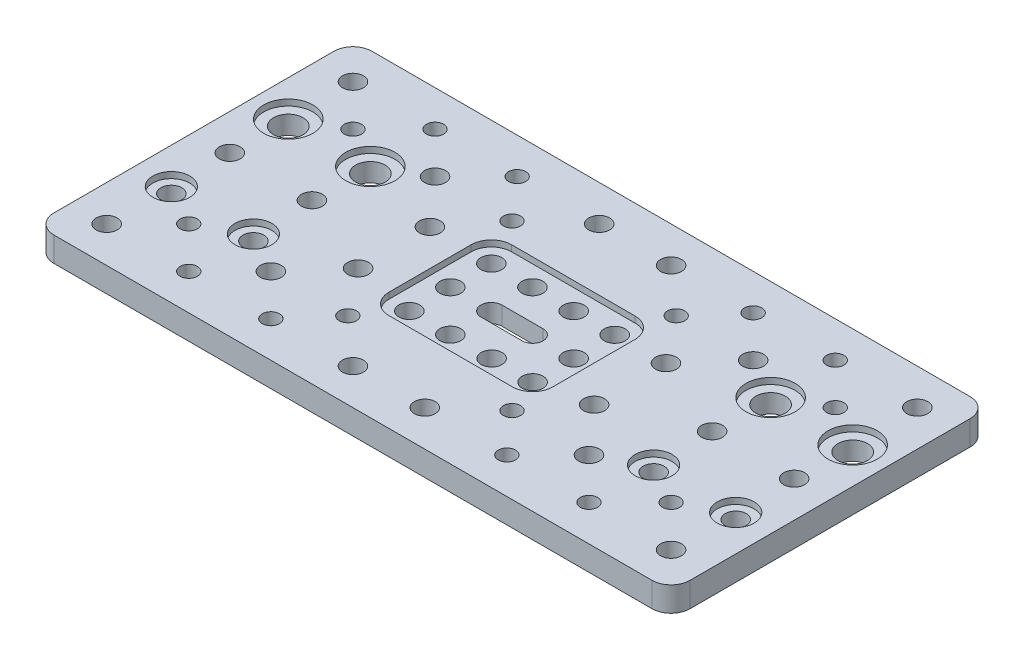
SolidWorks part; units mm, degrees
material "6061-T6 (SS)"
ref_plane "Front Plane" through (0, 0, 0) normal (0, 0, 1) x (1, 0, 0)
ref_plane "Top Plane" through (0, 0, 0) normal (0, 1, 0) x (1, 0, 0)
ref_plane "Right Plane" through (0, 0, 0) normal (1, 0, 0) x (0, 0, -1)
sketch "Sketch1" plane through (0, 0, 0) normal (0, 1, 0) x (1, 0, 0)
  line L1 (4.64, 0) -> (150.38, 0)
  line L2 (0, 4.64) -> (0, 72.88)
  line L3 (4.64, 77.52) -> (150.38, 77.52)
  line L4 (155.02, 4.64) -> (155.02, 72.88)
  arc A0 (150.38, 0) -> (155.02, 4.64) centre (150.38, 4.64) ccw
  arc A1 (150.38, 77.52) -> (155.02, 72.88) centre (150.38, 72.88) cw
  arc A2 (0, 72.88) -> (4.64, 77.52) centre (4.64, 72.88) cw
  arc A3 (4.64, 0) -> (0, 4.64) centre (4.64, 4.64) cw
  point P9 (155.02, 77.52)
  point P12 (0, 77.52)
  point P15 (0, 0)
  dimension "D3" = 4.64
  dimension "D1" = 77.52
  dimension "D2" = 155.02
extrude "Boss-Extrude1" add sketch "Sketch1" along normal blind 6
hole_wizard "Ø5.1 (5.1) Diameter Hole1" positions "Sketch3" profile "Sketch2" hole size "Ø5.1" standard "ANSI Metric" end condition through all
sketch "Sketch3" plane through (0, 6, 0) normal (0, 1, 0) x (1, 0, 0)
  line L0 (0, 38.76) -> (77.51, 38.76) construction
  line L1 (0, 72.88) -> (0, 4.64) construction
  line L2 (77.51, 38.76) -> (77.51, 77.52) construction
  line L3 (150.38, 77.52) -> (4.64, 77.52) construction
  point P0 (8.755, 68.76)
  point P2 (8.755, 38.76)
  point P4 (28.755, 38.76)
  point P6 (38.755, 58.76)
  point P8 (48.755, 47.515)
  point P10 (68.755, 68.76)
  point P12 (62.485, 48.76)
  point P14 (72.485, 48.76)
  point P16 (62.485, 38.76)
  point P36 (92.535, 38.76)
  point P37 (82.535, 48.76)
  point P38 (92.535, 48.76)
  point P39 (86.265, 68.76)
  point P40 (106.265, 47.515)
  point P41 (116.265, 58.76)
  point P42 (126.265, 38.76)
  point P43 (146.265, 38.76)
  point P44 (146.265, 68.76)
  point P47 (146.265, 8.76)
  point P48 (116.265, 18.76)
  point P49 (106.265, 30.005)
  point P50 (92.535, 28.76)
  point P51 (82.535, 28.76)
  point P52 (86.265, 8.76)
  point P53 (68.755, 8.76)
  point P54 (72.485, 28.76)
  point P55 (62.485, 28.76)
  point P56 (48.755, 30.005)
  point P57 (38.755, 18.76)
  point P58 (8.755, 8.76)
  dimension "D1" = 10
  dimension "D2" = 10
  dimension "D3" = 17.51
  dimension "D4" = 30
  dimension "D5" = 30
  dimension "D6" = 20
  dimension "D7" = 10.05
  dimension "D8" = 17.51
  dimension "D9" = 60
  dimension "D10" = 20
  dimension "D11" = 10
sketch "Sketch2" plane through (8.755, 6, -68.76) normal (1, 0, 0) x (0, 0, 1)
  line L0 (0, 0) -> (0, 6)
  line L1 (0, 6) -> (2.55, 6)
  line L2 (2.55, 6) -> (2.55, 0)
  line L5 (2.55, 0) -> (0, 0)
  line L11 (0, -6.35) -> (0, 107.95) construction
  dimension "Thru Hole Dia." = 5.1
  dimension "Thru Hole Depth" = 6
hole_wizard "M5x0.8 Tapped Hole1" positions "Sketch5" profile "Sketch4" tap size "M5x0.8" standard "ANSI Metric" end condition through all
sketch "Sketch5" plane through (0, 6, 0) normal (0, 1, 0) x (1, 0, 0)
  line L0 (0, 38.76) -> (77.51, 38.76) construction
  line L1 (0, 72.88) -> (0, 4.64) construction
  line L2 (77.51, 38.76) -> (77.51, 77.52) construction
  line L3 (150.38, 77.52) -> (4.64, 77.52) construction
  circle A0 centre (8.755, 68.76) radius 2.55 construction
  point P0 (18.75, 58.76)
  point P2 (28.755, 68.76)
  point P4 (48.755, 68.76)
  point P6 (57.51, 58.76)
  point P23 (48.755, 8.76)
  point P24 (57.51, 18.76)
  point P25 (18.75, 18.76)
  point P26 (28.755, 8.76)
  point P28 (106.265, 68.76)
  point P29 (97.51, 58.76)
  point P30 (97.51, 18.76)
  point P31 (106.265, 8.76)
  point P32 (126.265, 8.76)
  point P33 (136.27, 18.76)
  point P34 (126.265, 68.76)
  point P35 (136.27, 58.76)
  dimension "D5" = 20
  dimension "D1" = 20
  dimension "D2" = 40
  dimension "D3" = 60
  dimension "D4" = 40
  dimension "D6" = 38.76
sketch "Sketch4" plane through (18.75, 6, -58.76) normal (1, 0, 0) x (0, 0, 1)
  line L0 (0, 0) -> (0, 6)
  line L1 (0, 6) -> (2.1, 6)
  line L2 (2.1, 6) -> (2.1, 0)
  line L5 (2.1, 0) -> (0, 0)
  line L11 (0, -6.35) -> (0, 107.95) construction
  dimension "Thread Major Dia." = 4.2
  dimension "Thru Tap Drill Depth" = 6
sketch "Sketch6" plane through (0, 6, 0) normal (0, 1, 0) x (1, 0, 0)
  line L0 (77.51, 77.52) -> (77.51, 95.8918) construction
  line L1 (150.38, 77.52) -> (4.64, 77.52) construction
  line L2 (0, 38.76) -> (-8.4214, 38.76) construction
  line L3 (0, 72.88) -> (0, 4.64) construction
  line L4 (8.755, 68.76) -> (8.755, 53.01) construction
  circle A0 centre (8.755, 53.01) radius 3.6
  circle A1 centre (28.755, 53.01) radius 3.6
  circle A2 centre (8.755, 24.51) radius 2.55
  circle A3 centre (28.755, 24.51) radius 2.55
  circle A4 centre (126.265, 24.51) radius 2.55
  circle A5 centre (146.265, 24.51) radius 2.55
  circle A6 centre (126.265, 53.01) radius 3.6
  circle A7 centre (146.265, 53.01) radius 3.6
  dimension "D1" = 7.2
  dimension "D2" = 5.1
  dimension "D3" = 28.5
  dimension "D4" = 20
extrude "Cut-Extrude1" cut sketch "Sketch6" against normal through all
sketch "Sketch7" plane through (0, 6, 0) normal (0, 1, 0) x (1, 0, 0)
  line L0 (77.51, 77.52) -> (77.51, 38.76) construction
  line L1 (150.38, 77.52) -> (4.64, 77.52) construction
  line L2 (57.535, 23.81) -> (97.485, 53.71) construction
  line L3 (62.475, 53.71) -> (92.545, 53.71)
  line L4 (57.535, 48.77) -> (57.535, 28.75)
  line L5 (62.475, 23.81) -> (92.545, 23.81)
  line L6 (97.485, 48.77) -> (97.485, 28.75)
  line L7 (77.51, 38.76) -> (155.02, 38.76) construction
  line L8 (155.02, 4.64) -> (155.02, 72.88) construction
  circle A0 centre (8.755, 53.01) radius 6
  circle A1 centre (28.755, 53.01) radius 6
  circle A2 centre (8.755, 24.51) radius 4.5
  circle A3 centre (28.755, 24.51) radius 4.5
  circle A4 centre (126.265, 24.51) radius 4.5
  circle A5 centre (146.265, 24.51) radius 4.5
  circle A6 centre (126.265, 53.01) radius 6
  circle A7 centre (146.265, 53.01) radius 6
  arc A8 (92.545, 53.71) -> (97.485, 48.77) centre (92.545, 48.77) cw
  arc A9 (62.475, 53.71) -> (57.535, 48.77) centre (62.475, 48.77) ccw
  arc A10 (57.535, 28.75) -> (62.475, 23.81) centre (62.475, 28.75) ccw
  arc A11 (92.545, 23.81) -> (97.485, 28.75) centre (92.545, 28.75) ccw
  point P28 (77.51, 38.76)
  dimension "D1" = 12
  dimension "D2" = 9
  dimension "D5" = 4.94
  dimension "D3" = 39.95
  dimension "D4" = 29.9
extrude "Cut-Extrude2" cut sketch "Sketch7" against normal blind 1.5
sketch "Sketch8" plane through (0, 4.5, 0) normal (0, 1, 0) x (1, 0, 0)
  line L0 (72.485, 38.76) -> (82.535, 38.76) construction
  line L1 (72.485, 41.31) -> (82.535, 41.31)
  line L2 (72.485, 36.21) -> (82.535, 36.21)
  line L3 (77.51, 38.76) -> (77.51, 53.71) construction
  line L4 (92.545, 53.71) -> (62.475, 53.71) construction
  line L5 (72.485, 38.76) -> (57.535, 38.76) construction
  line L6 (57.535, 48.77) -> (57.535, 28.75) construction
  arc A0 (72.485, 41.31) -> (72.485, 36.21) centre (72.485, 38.76) ccw
  arc A1 (82.535, 36.21) -> (82.535, 41.31) centre (82.535, 38.76) ccw
  point P2 (77.51, 38.76)
  dimension "D1" = 10.05
  dimension "D2" = 5.1
extrude "Cut-Extrude3" cut sketch "Sketch8" against normal through all
ref_plane "Plane1" through (0, 0, -38.76) normal (0, 0, -1) x (-1, 0, 0)
